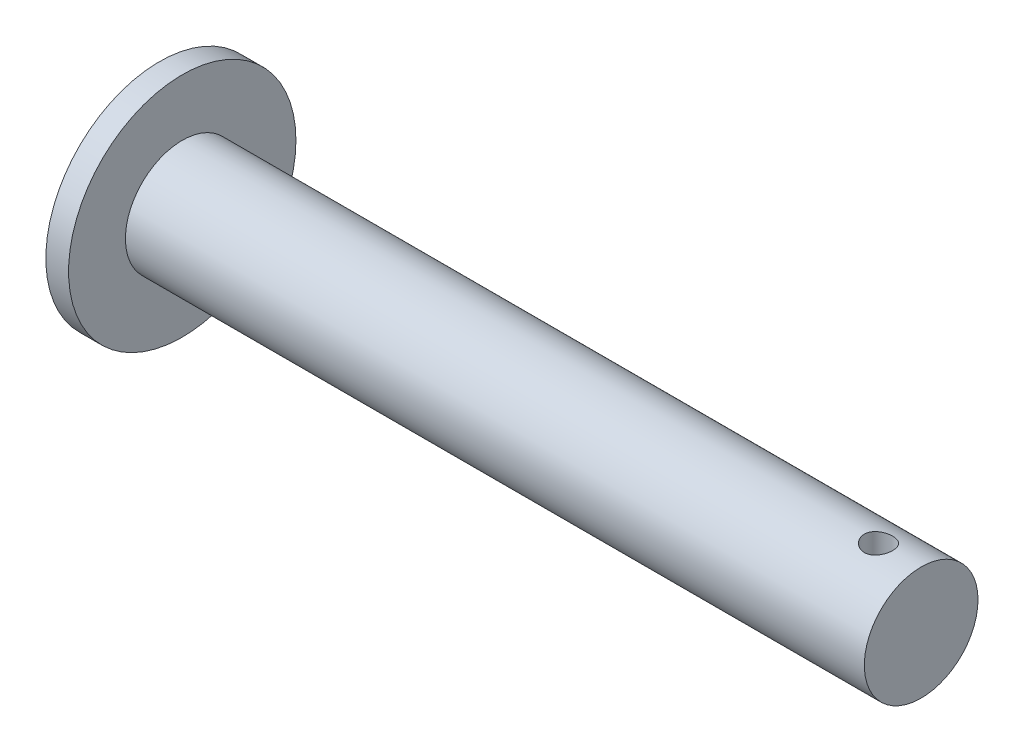
SolidWorks part; units mm, degrees
ref_plane "Front Plane" through (0, 0, 0) normal (0, 0, 1) x (1, 0, 0)
ref_plane "Top Plane" through (0, 0, 0) normal (0, 1, 0) x (1, 0, 0)
ref_plane "Right Plane" through (0, 0, 0) normal (1, 0, 0) x (0, 0, -1)
sketch "Sketch1" plane through (0, 0, 0) normal (1, 0, 0) x (0, 0, -1)
  circle A0 centre (0, 0) radius 12.7
extrude "Boss-Extrude1" add sketch "Sketch1" along normal blind 2.54
sketch "Sketch2" plane through (2.54, 0, 0) normal (1, 0, 0) x (0, 0, -1)
  circle A0 centre (0, 0) radius 6.35
extrude "Boss-Extrude2" add sketch "Sketch2" along normal blind 82.55
sketch "Sketch3" plane through (0, 0, 0) normal (0, 1, 0) x (1, 0, 0)
  line L0 (2.54, -6.35) -> (2.54, 6.35) construction
  circle A0 centre (80.3275, 0) radius 1.5875
  dimension "D2" = 3.175
  dimension "D1" = 77.7875
extrude "Cut-Extrude1" cut sketch "Sketch3" against normal mid plane 25.4
